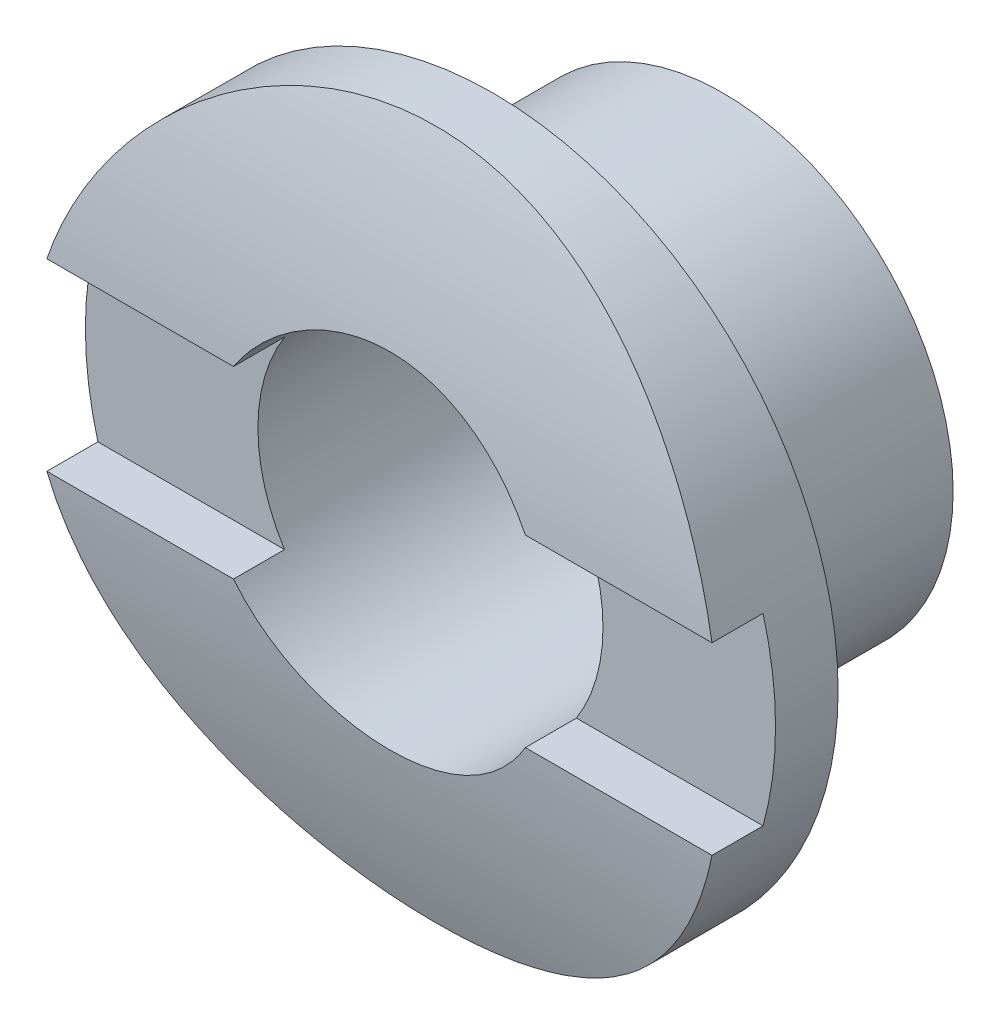
SolidWorks part; units mm, degrees
ref_plane "Front Plane" through (0, 0, 0) normal (0, 0, 1) x (1, 0, 0)
ref_plane "Top Plane" through (0, 0, 0) normal (0, 1, 0) x (1, 0, 0)
ref_plane "Right Plane" through (0, 0, 0) normal (1, 0, 0) x (0, 0, -1)
sketch "Sketch1" plane through (0, 0, 0) normal (0, 0, 1) x (1, 0, 0)
  circle A0 centre (0, 0) radius 3.175
  circle A1 centre (0, 0) radius 2.3813
  dimension "D1" = 4.7625
  dimension "D3" = 6.35
extrude "Boss-Extrude1" add sketch "Sketch1" along normal blind 3.175 contours A0
sketch "Sketch2" plane through (0, 0, 3.175) normal (0, 0, 1) x (1, 0, 0)
  circle A0 centre (0, 0) radius 4.7625
  circle A1 centre (0, 0) radius 2.3813
  dimension "D1" = 9.525
  dimension "D2" = 4.7625
extrude "Boss-Extrude2" add sketch "Sketch2" along normal blind 1.6256
sketch "Sketch3" plane through (0, 0, 0) normal (1, 0, 0) x (0, 0, -1)
  line L0 (-4.8006, 0) -> (9.1694, 0) construction
  line L1 (-4.8006, 4.7625) -> (-4.8006, -4.7625) construction
  circle A0 centre (9.1694, 0) radius 13.97
  circle A1 centre (9.1694, 0) radius 22.3612
  dimension "D1" = 13.97
extrude "Cut-Extrude1" cut sketch "Sketch3" against normal through all and the other way through all
sketch "Sketch4" plane through (0, 0, 0) normal (1, 0, 0) x (0, 0, -1)
  line L1 (-4.8006, 1.27) -> (-4.0386, 1.27)
  line L2 (-4.8006, 1.27) -> (-4.8006, -1.27)
  line L3 (-4.8006, -1.27) -> (-4.0386, -1.27)
  line L4 (-4.0386, 1.27) -> (-4.0386, -1.27)
  arc A1 (-3.9637, 4.7625) -> (-3.9637, -4.7625) centre (9.1694, 0) ccw construction
  point P4 (-4.0386, 0)
  dimension "D1" = 0.762
  dimension "D2" = 2.54
extrude "Cut-Extrude2" cut sketch "Sketch4" against normal through all both and the other way through all
